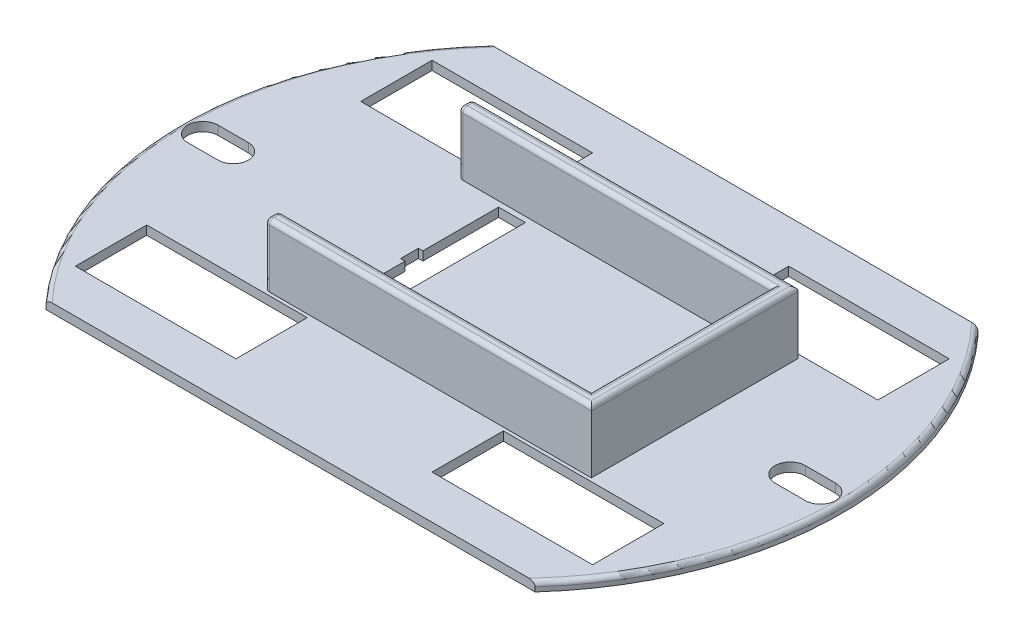
SolidWorks part; units mm, degrees
ref_plane "Płaszczyzna przednia" through (0, 0, 0) normal (0, 0, 1) x (1, 0, 0)
ref_plane "Płaszczyzna górna" through (0, 0, 0) normal (0, 1, 0) x (1, 0, 0)
ref_plane "Płaszczyzna prawa" through (0, 0, 0) normal (1, 0, 0) x (0, 0, -1)
sketch "Sketch1" plane through (0, 0, 0) normal (0, 1, 0) x (1, 0, 0)
  line L8 (0, 0) -> (0, 37)
  line L9 (0, 0) -> (0, -37)
  line L11 (0, 37) -> (0, 24.8373)
  line L14 (0, 24.8373) -> (27.4246, 24.8373)
  line L15 (27.4246, 24.8373) -> (-27.4246, 24.8373)
  line L16 (27.4246, 24.8373) -> (27.4246, -24.8373)
  line L17 (27.4246, -24.8373) -> (-27.4246, -24.8373)
  circle A0 centre (0, 0) radius 37
  point P0 (0, 0)
extrude "Boss-Extrude1" add sketch "Sketch1" along normal blind 2
sketch "Sketch2" plane through (0, 0, 0) normal (0, -1, 0) x (1, 0, 0)
  line L0 (0, 0) -> (-8, 0)
  line L6 (-8, 0) -> (-8, 9.5)
  line L7 (-8, 9.5) -> (-11, 9.5)
  line L8 (-11, 9.5) -> (-11, -9.5)
  line L9 (-11, -9.5) -> (-8, -9.5)
  line L10 (-8, -9.5) -> (-8, 0)
  line L11 (-8, 0) -> (-8, 1)
  line L12 (-8, 1) -> (-11.5, 1)
  line L13 (-11.5, 1) -> (-11.5, -1)
  line L14 (-11.5, -1) -> (-8, -1)
  line L15 (-8, -1) -> (-8, 1)
extrude "Cut-Extrude1" cut sketch "Sketch2" against normal blind 22 contours L6 L7 L8 L9 L10 | L12 L13 L14 L15
sketch "Sketch3" plane through (0, 2, 0) normal (0, 1, 0) x (1, 0, 0)
  line L0 (2.9, 0) -> (2.9, 10.1)
  line L1 (2.9, 10.1) -> (19, 10.1)
  line L2 (19, 10.1) -> (19, -10.1)
  line L3 (19, -10.1) -> (-14.6, -10.1)
  line L4 (-14.6, -10.1) -> (-14.6, 10.1)
  line L5 (-14.6, 10.1) -> (2.9, 10.1)
  line L6 (2.9, 10.1) -> (2.9, 11.6)
  line L7 (19, 10.1) -> (20.5, 10.1)
  line L8 (19, -10.1) -> (19, -11.6)
  line L9 (-14.6, -10.1) -> (-16.1, -10.1)
  line L10 (2.9, 11.6) -> (20.5, 11.6)
  line L11 (20.5, 11.6) -> (20.5, -11.6)
  line L12 (20.5, -11.6) -> (-16.1, -11.6)
  line L13 (-16.1, -11.6) -> (-16.1, 11.6)
  line L14 (-16.1, 11.6) -> (2.9, 11.6)
  line L15 (-14.6, 10.1) -> (-16.1, 10.1)
extrude "Boss-Extrude2" add sketch "Sketch3" along normal blind 7 contours L11 L10 L6 L1 L7 | L12 L11 L7 L2 L8 | L13 L12 L8 L3 L9 | L15 L5 L6 L14 L13
sketch "Sketch4" plane through (0, 0, 0) normal (0, -1, 0) x (1, 0, 0)
  line L0 (0, 0) -> (-8, 0)
  line L1 (-8, -9.5) -> (-8, 9.5) construction
  line L2 (-8, 0) -> (-8.023, 9.319)
  line L3 (-8.023, 9.319) -> (-3, 9.319)
  line L4 (-3, 9.319) -> (-3, -9.5)
  line L5 (-3, -9.5) -> (-8, -9.5)
  line L6 (-8, -9.5) -> (-8, 0)
extrude "Boss-Extrude3" add sketch "Sketch4" along normal blind 6 contours L2 L3 L4 L5 L6
sketch "Sketch5" plane through (-8, 0, 0) normal (-1, 0, 0) x (0, 0, 1)
  line L0 (0, 0) -> (0, -6)
  line L3 (-24.8373, 0) -> (24.8373, 0) construction
  line L5 (0, -6) -> (0, 0) construction
  circle A1 centre (-5.031, -2.35) radius 2.25
  circle A4 centre (5.031, -2.35) radius 2.25
extrude "Cut-Extrude3" cut sketch "Sketch5" against normal blind 37 and the other way blind 37 contours A1 | A4
fillet "Fillet1" radius 3 2 edges at (-5.5, -6, -9.5) (-5.5115, -6, 9.319)
fillet "Fillet2" radius 0.5 2 edges at (-37, 2, 0) (37, 2, 0)
sketch "Sketch6" plane through (0, 0, 0) normal (0, -1, 0) x (1, 0, 0)
  line L0 (0.0031, -0.031) -> (-32.9969, -0.031)
  line L1 (0.0031, -0.031) -> (-0.0115, 6.969)
  line L2 (-32.9969, -0.031) -> (-34.6969, -0.031)
  line L3 (-34.6969, -0.031) -> (-31.2969, -0.031)
  line L4 (-34.6969, 1.669) -> (-31.2969, 1.669)
  line L5 (-34.6969, -1.731) -> (-31.2969, -1.731)
  line L6 (33.0028, 0.1067) -> (0.0031, -0.031)
  line L7 (31.3028, 1.8067) -> (34.7028, 1.8067)
  line L9 (34.7028, -1.5933) -> (31.3028, -1.5933)
  circle A0 centre (-32.9969, -0.031) radius 1.7
  circle A1 centre (33.0028, 0.1067) radius 1.7
  circle A2 centre (-31.2969, -0.031) radius 1.7
  circle A3 centre (-34.6969, -0.031) radius 1.7
  arc A4 (-31.2969, 1.669) -> (-31.2969, -1.731) centre (-31.2969, -0.031) cw
  arc A5 (-34.6969, 1.669) -> (-34.6969, -1.731) centre (-34.6969, -0.031) ccw
  circle A8 centre (31.3028, 0.1067) radius 1.7
  circle A9 centre (34.7028, 0.1067) radius 1.7
  arc A10 (31.3028, 1.8067) -> (31.3028, -1.5933) centre (31.3028, 0.1067) ccw
  arc A15 (34.7028, 1.8067) -> (34.7028, -1.5933) centre (34.7028, 0.1067) cw
  dimension "D1" = 33
extrude "Cut-Extrude4" cut sketch "Sketch6" against normal blind 37 contours A1
fillet "Fillet3" radius 0.5 6 edges at (20.5, 9, 0) (19, 9, 0) (1.45, 9, -10.1) (2.2, 9, -11.6) (2.2, 9, 11.6) (1.45, 9, 10.1)
fillet "Fillet4" radius 0.5 10 edges at (-16.1, 5.25, 11.6) (-16.1, 8.8536, 11.4536) (-16.1, 9, 10.85) (-16.1, 8.8536, 10.2464) (-16.1, 5.25, -10.1) (-16.1, 8.8536, -10.2464) (-16.1, 9, -10.85) (-16.1, 8.8536, -11.4536) (-16.1, 5.25, 10.1) (-16.1, 5.25, -11.6)
sketch "Sketch7" plane through (0, 0, 0) normal (0, -1, 0) x (1, 0, 0)
  line L0 (0.0031, -0.031) -> (20.0031, -0.031)
  line L1 (20.0031, -0.031) -> (20.0031, 14.969)
  line L2 (20.0031, 14.969) -> (20.0031, 19.969)
  line L3 (20.0031, 19.969) -> (11.0031, 19.969)
  line L4 (11.0031, 19.969) -> (11.0031, 11.969)
  line L5 (11.0031, 11.969) -> (29.0031, 11.969)
  line L6 (29.0031, 11.969) -> (29.0031, 19.969)
  line L7 (29.0031, 19.969) -> (20.0031, 19.969)
  line L8 (0.0031, -0.031) -> (0.0031, 13.3164)
  line L9 (29.0031, -20.031) -> (20.0031, -20.031)
  line L10 (29.0031, -12.031) -> (29.0031, -20.031)
  line L11 (11.0031, -12.031) -> (29.0031, -12.031)
  line L12 (11.0031, -20.031) -> (11.0031, -12.031)
  line L13 (20.0031, -20.031) -> (11.0031, -20.031)
  line L14 (-28.9969, -12.031) -> (-28.9969, -20.031)
  line L15 (-10.9969, -12.031) -> (-28.9969, -12.031)
  line L16 (-10.9969, -20.031) -> (-10.9969, -12.031)
  line L17 (-19.9969, -20.031) -> (-10.9969, -20.031)
  line L18 (-28.9969, -20.031) -> (-19.9969, -20.031)
  line L19 (-28.9969, 19.969) -> (-19.9969, 19.969)
  line L20 (-28.9969, 11.969) -> (-28.9969, 19.969)
  line L21 (-10.9969, 11.969) -> (-28.9969, 11.969)
  line L22 (-10.9969, 19.969) -> (-10.9969, 11.969)
  line L23 (-19.9969, 19.969) -> (-10.9969, 19.969)
extrude "Cut-Extrude5" cut sketch "Sketch7" against normal blind 10 contours L23 L19 L20 L21 L22 | L4 L5 L1 L2 L3 | L6 L7 L2 L1 L5 | L14 L18 L17 L16 L15 | L13 L9 L10 L11 L12
fillet "Fillet8" radius 1 16 edges at (11.0031, 0, 15.969) (20.0031, 0, 11.969) (29.0031, 0, 15.969) (20.0031, 0, 19.969) (20.0031, 0, -12.031) (29.0031, 0, -16.031) (20.0031, 0, -20.031) (11.0031, 0, -16.031) (-10.9969, 0, 15.969) (-19.9969, 0, 19.969) (-28.9969, 0, 15.969) (-19.9969, 0, 11.969) (-28.9969, 0, -16.031) (-19.9969, 0, -12.031) (-19.9969, 0, -20.031) (-10.9969, 0, -16.031)
sketch "Sketch8" plane through (0, 0, 24.8373) normal (0, 0, 1) x (1, 0, 0)
  line L0 (0, 0) -> (0, 1)
  line L1 (0, 1) -> (46.8329, 1)
  line L2 (46.8329, 1) -> (-54.4517, 1)
  line L3 (0, 0) -> (-0.1, 0)
  line L4 (27.4246, 0) -> (-27.4246, 0) construction
  line L5 (-0.1, 0) -> (-0.1, 1)
  line L6 (-0.1, 1) -> (0.1, 1)
  line L7 (0.1, 1) -> (0.1, 0)
  line L8 (0.1, 0) -> (-0.1, 0)
  line M6 (-27.4246, 0) -> (27.4246, 0)
extrude "Cut-Extrude6" cut sketch "Sketch8" against normal blind 0.1 contours L5 L0 L2 M6 | L7 L1 L0 M6
sketch "Sketch10" plane through (0, 0, 0) normal (0, -1, 0) x (1, 0, 0)
  circle A0 centre (0, 0) radius 57.5567
extrude "Cut-Extrude7" cut sketch "Sketch10" against normal blind 1 and the other way blind 11
